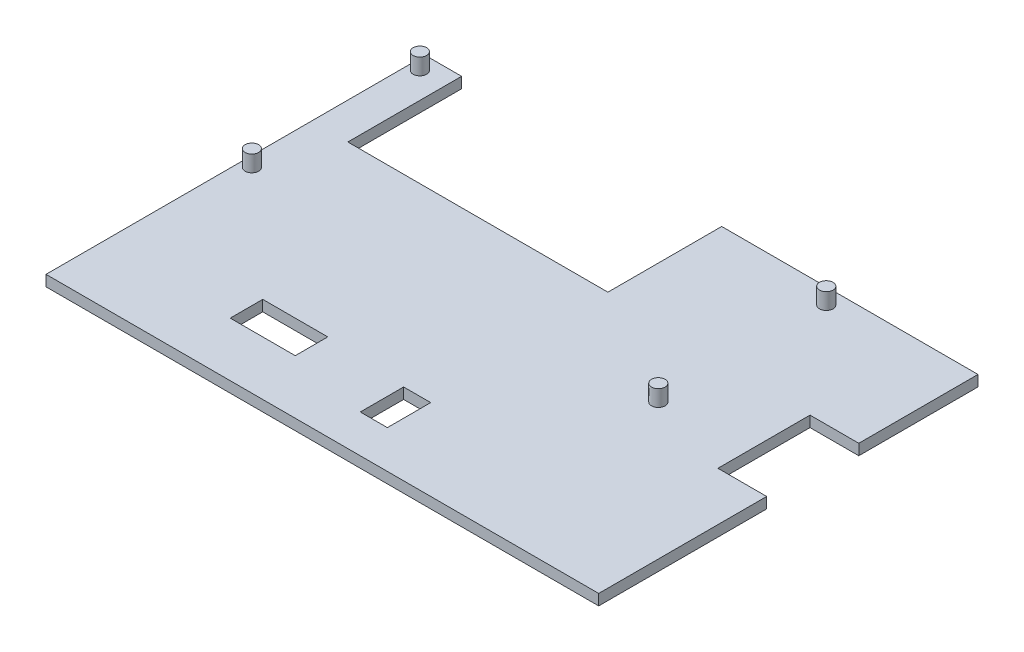
SolidWorks part; units mm, degrees
ref_plane "Alzado" through (0, 0, 0) normal (0, 0, 1) x (1, 0, 0)
ref_plane "Planta" through (0, 0, 0) normal (0, 1, 0) x (1, 0, 0)
ref_plane "Vista lateral" through (0, 0, 0) normal (1, 0, 0) x (0, 0, -1)
sketch "Croquis1" plane through (0, 0, 0) normal (0, 1, 0) x (1, 0, 0)
  line L0 (0, 70) -> (6.7, 70)
  line L1 (0, 0) -> (102, 0)
  line L2 (0, 0) -> (0, 70)
  line L3 (0, 70) -> (102, 70) construction
  line L4 (102, 0) -> (102, 70) construction
  line L5 (6.7, 70) -> (6.7, 49)
  line L6 (6.7, 49) -> (54.7, 49)
  line L7 (54.7, 49) -> (54.7, 70)
  line L8 (54.7, 70) -> (102, 70)
  line L9 (102, 70) -> (102, 48)
  line L10 (102, 48) -> (93, 48)
  line L11 (93, 48) -> (93, 31)
  line L12 (93, 31) -> (102, 31)
  line L13 (102, 31) -> (102, 0)
  line L15 (24, 16) -> (36, 16)
  line L16 (24, 16) -> (24, 10)
  line L17 (24, 10) -> (36, 10)
  line L18 (36, 16) -> (36, 10)
  line L19 (51, 15) -> (56, 15)
  line L20 (51, 15) -> (51, 7)
  line L21 (51, 7) -> (56, 7)
  line L22 (56, 15) -> (56, 7)
  dimension "D1" = 102
  dimension "D2" = 70
  dimension "D3" = 6.7
  dimension "D4" = 48
  dimension "D5" = 21
  dimension "D6" = 9
  dimension "D7" = 17
  dimension "D8" = 22
  dimension "D9" = 24
  dimension "D10" = 10
  dimension "D11" = 12
  dimension "D12" = 6
  dimension "D13" = 7
  dimension "D14" = 51
  dimension "D15" = 5
  dimension "D16" = 8
extrude "Saliente-Extruir1" add sketch "Croquis1" along normal blind 2
sketch "Croquis2" plane through (0, 2, 0) normal (0, 1, 0) x (1, 0, 0)
  line L0 (0, 70) -> (0, 0) construction
  line L1 (1.9, 67.1) -> (76.9, 67.1) construction
  line L2 (1.9, 67.1) -> (1.9, 36.1) construction
  line L3 (1.9, 36.1) -> (76.9, 36.1) construction
  line L4 (76.9, 67.1) -> (76.9, 36.1) construction
  line L5 (6.7, 70) -> (0, 70) construction
  circle A0 centre (1.9, 67.1) radius 1.25
  circle A1 centre (1.9, 36.1) radius 1.25
  circle A2 centre (76.9, 36.1) radius 1.25
  circle A3 centre (76.9, 67.1) radius 1.25
  dimension "D1" = 2.5
  dimension "D2" = 75
  dimension "D3" = 31
  dimension "D4" = 1.9
  dimension "D5" = 2.9
extrude "Saliente-Extruir2" add sketch "Croquis2" along normal blind 3
